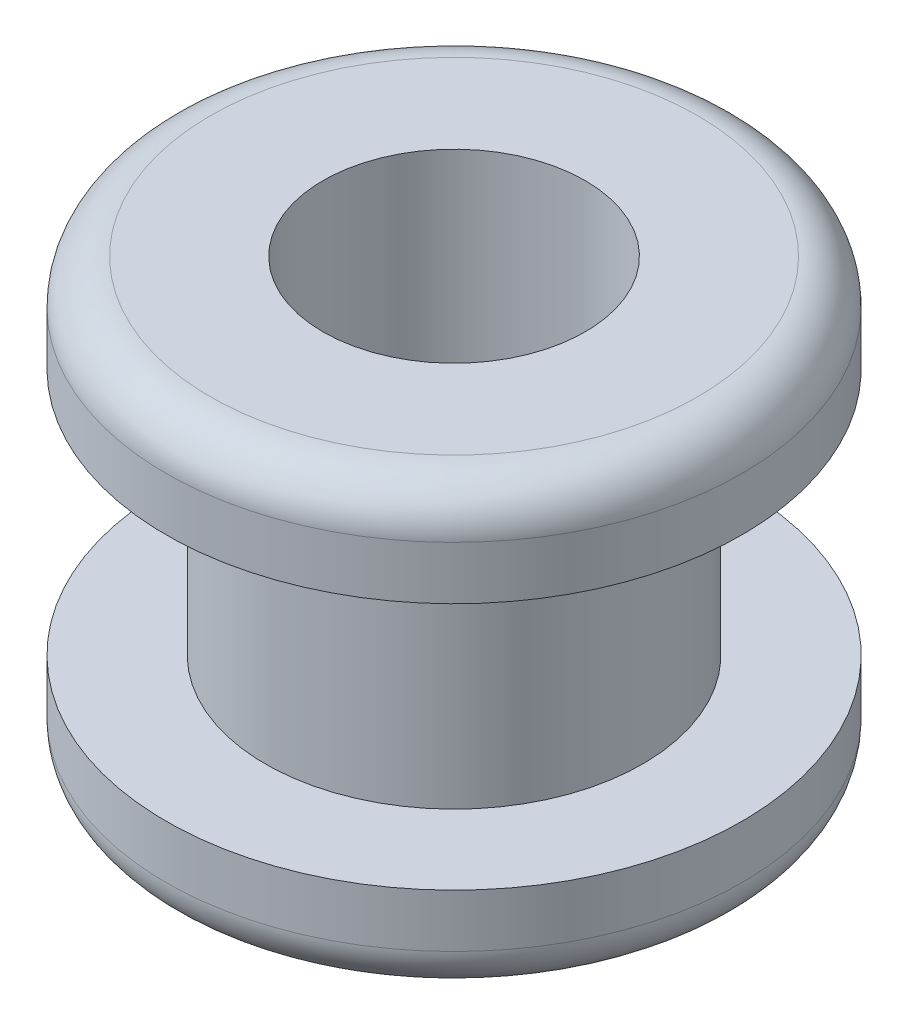
SolidWorks part; units mm, degrees
material "Caoutchouc"
ref_plane "Plan de face" through (0, 0, 0) normal (0, 0, 1) x (1, 0, 0)
ref_plane "Plan de dessus" through (0, 0, 0) normal (0, 1, 0) x (1, 0, 0)
ref_plane "Plan de droite" through (0, 0, 0) normal (1, 0, 0) x (0, 0, -1)
sketch "Esquisse1" plane through (0, 0, 0) normal (0, 0, 1) x (1, 0, 0)
  line L0 (0, 0) -> (0, 4.3316) construction
  line L1 (-3.25, -1.4) -> (-3.25, -2)
  line L2 (-2.75, 2.5) -> (-1.48, 2.5)
  line L3 (-3.25, 2) -> (-3.25, 1.4)
  line L4 (-2.75, -2.5) -> (-1.48, -2.5)
  line L5 (-1.48, 2.5) -> (-1.48, -2.5)
  line L6 (-3.25, 1.4) -> (-2.13, 1.4)
  line L7 (-1.48, 0) -> (0, 0) construction
  line L8 (-3.25, -1.4) -> (-2.13, -1.4)
  line L9 (-2.13, 1.4) -> (-2.13, -1.4)
  arc A0 (-3.25, -2) -> (-2.75, -2.5) centre (-2.75, -2) ccw
  arc A1 (-2.75, 2.5) -> (-3.25, 2) centre (-2.75, 2) ccw
  dimension "D6" = 0.5
  dimension "D1" = 6.5
  dimension "D2" = 5
  dimension "D3" = 4.26
  dimension "D4" = 2.96
  dimension "D5" = 2.8
  dimension "D7" = 1.1
revolve "Révolution1" add sketch "Esquisse1" angle 360 about L0
